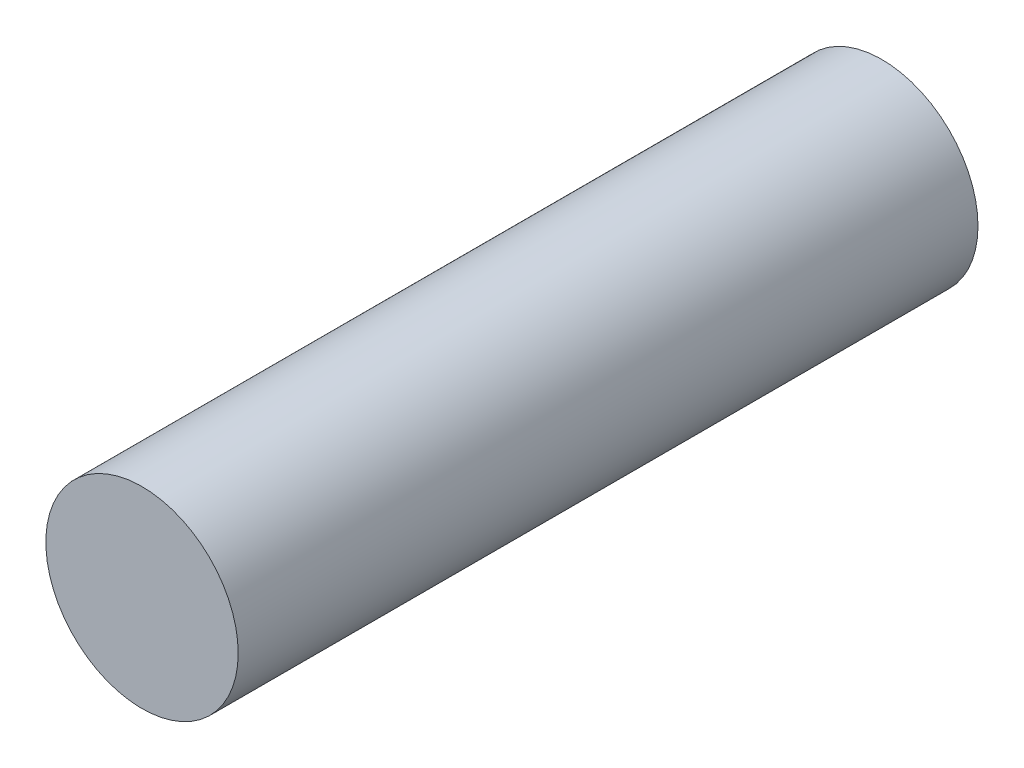
SolidWorks part; units mm, degrees
ref_plane "Front Plane" through (0, 0, 0) normal (0, 0, 1) x (1, 0, 0)
ref_plane "Top Plane" through (0, 0, 0) normal (0, 1, 0) x (1, 0, 0)
ref_plane "Right Plane" through (0, 0, 0) normal (1, 0, 0) x (0, 0, -1)
sketch "Sketch1" plane through (0, 0, 0) normal (0, 0, 1) x (1, 0, 0)
  circle A0 centre (0, 0) radius 0.65
  dimension "D1" = 1.3
extrude "Extrude1" add sketch "Sketch1" along normal blind 5
